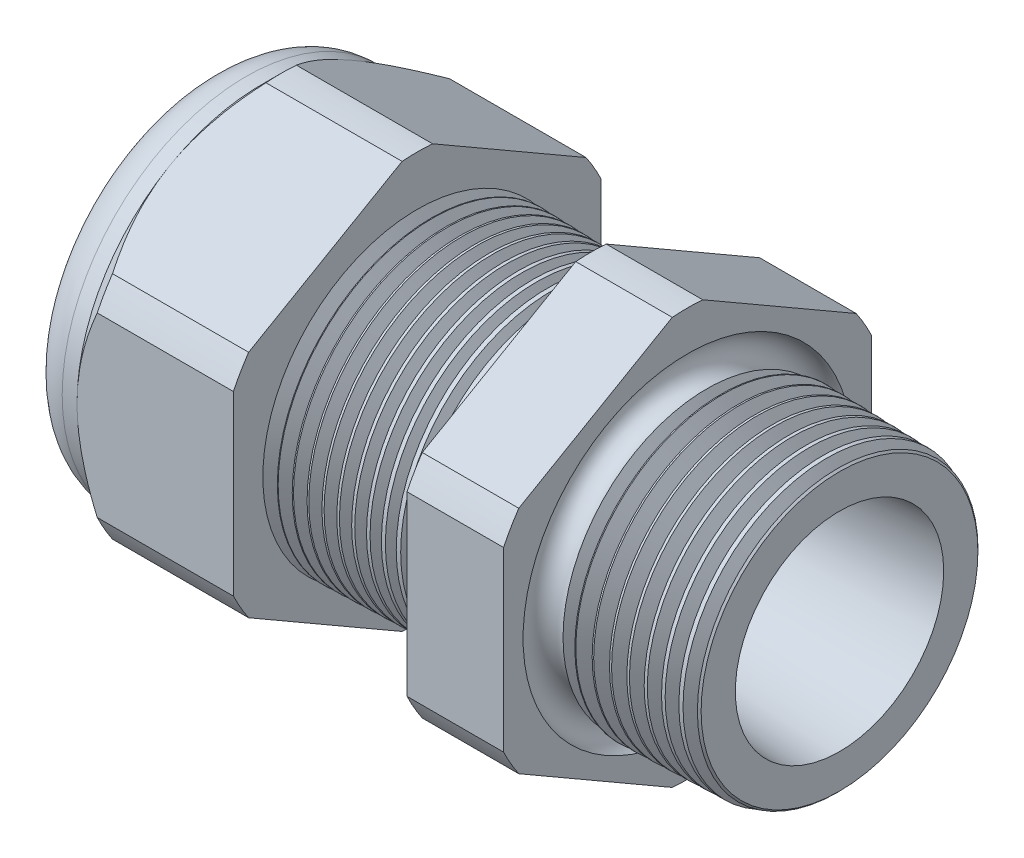
SolidWorks part; units mm, degrees
ref_plane "Front Plane" through (0, 0, 0) normal (0, 0, 1) x (1, 0, 0)
ref_plane "Top Plane" through (0, 0, 0) normal (0, 1, 0) x (1, 0, 0)
ref_plane "Right Plane" through (0, 0, 0) normal (1, 0, 0) x (0, 0, -1)
sketch "Sketch10" plane through (0, 0, 0) normal (0, 0, 1) x (1, 0, 0)
  line L0 (0, 0) -> (-115.3565, 0) construction
  line L1 (-32.766, 3.937) -> (-21.866, 3.937)
  line L2 (0, 5.3964) -> (0, 7.4284)
  line L3 (-7.874, 7.6346) -> (0, 7.4284)
  line L4 (-7.874, 19.05) -> (-7.874, 7.6346)
  line L5 (-7.874, 19.05) -> (-12.874, 19.05)
  line L6 (-12.874, 19.05) -> (-12.874, 7.7655)
  line L7 (-21.866, 8.001) -> (-12.874, 7.7655)
  line L8 (-21.866, 8.001) -> (-21.866, 19.05)
  line L9 (-21.866, 19.05) -> (-29.966, 19.05)
  line L10 (-29.966, 19.05) -> (-29.966, 9.525)
  line L11 (-29.966, 9.525) -> (-32.766, 9.525)
  line L12 (-32.766, 9.525) -> (-32.766, 3.937)
  line L13 (-21.866, 3.937) -> (0, 5.3964)
  dimension "D1" = 32.766
  dimension "D2" = 7.874
  dimension "D3" = 1.5
  dimension "D4" = 2.032
  dimension "A" = 16.002
  dimension "D6" = 19.05
  dimension "D8" = 38.1
  dimension "D9" = 2.8
  dimension "D10" = 8.1
  dimension "D11" = 5
  dimension "D" = 7.874
revolve "Revolve2" add sketch "Sketch10" angle 360 about L0
sketch "Sketch12" plane through (-29.966, 0, 0) normal (-1, 0, 0) x (0, 0, 1)
  line L1 (-0.7885, 10.5433) -> (-8.7365, 5.9545)
  line L2 (-9.525, 4.5888) -> (-9.525, -4.5888)
  line L3 (-8.7365, -5.9545) -> (-0.7885, -10.5433)
  line L4 (0.7885, -10.5433) -> (8.7365, -5.9545)
  line L5 (9.525, -4.5888) -> (9.525, 4.5888)
  line L6 (8.7365, 5.9545) -> (0.7885, 10.5433)
  circle A0 centre (0, 0) radius 9.525 construction
  arc A1 (0.7885, 10.5433) -> (-0.7885, 10.5433) centre (0, 0) ccw
  arc A2 (-8.7365, 5.9545) -> (-9.525, 4.5888) centre (0, 0) ccw
  arc A3 (-9.525, -4.5888) -> (-8.7365, -5.9545) centre (0, 0) ccw
  arc A4 (-0.7885, -10.5433) -> (0.7885, -10.5433) centre (0, 0) ccw
  arc A5 (8.7365, -5.9545) -> (9.525, -4.5888) centre (0, 0) ccw
  arc A6 (9.525, 4.5888) -> (8.7365, 5.9545) centre (0, 0) ccw
  dimension "D2" = 21.1455
  dimension "D1" = 19.05
extrude "Cut-Extrude2" cut sketch "Sketch12" against normal through all flip side to cut
fillet "Fillet4" radius 2.032 1 edges at (-32.766, 0, -9.525)
sketch "Sketch19" plane through (-29.966, 0, 0) normal (-1, 0, 0) x (0, 0, 1)
  line L0 (9.525, 0) -> (9.525, 4.5888) construction
  circle A0 centre (0, 0) radius 9.525
extrude "Cut-Extrude3" cut sketch "Sketch19" against normal blind 2 draft 45 flip side to cut
chamfer "Chamfer1" distance 0.254 angle 45 1 edges at (0, 0, -7.4284)
sketch "Sketch21" plane through (-32.766, 0, 0) normal (-1, 0, 0) x (0, 0, 1)
  circle A0 centre (0, 0) radius 3.937
  circle A2 centre (0, 0) radius 3.937 construction
extrude "plug" add sketch "Sketch21" against normal blind 3.81 separate body
sketch "Sketch22" plane through (-32.766, 0, 0) normal (-1, 0, 0) x (0, 0, 1)
  circle A0 centre (0, 0) radius 3.683
  circle A1 centre (0, 0) radius 3.937 construction
  dimension "D1" = 0.254
extrude "Cut-Extrude4" cut sketch "Sketch22" against normal blind 0.508
sketch "Sketch27" plane through (-32.258, 0, 0) normal (-1, 0, 0) x (0, 0, 1)
  line L0 (-4.3624, 0) -> (4.3624, 0) construction
  circle A0 centre (-1.8979, 0) radius 1.778
  circle A1 centre (0, 0) radius 3.683 construction
  dimension "D1" = 0.0071
  dimension "holedia" = 3.556
extrude "plugholes" cut sketch "Sketch27" against normal through all
pattern_circular "CirPattern1" count 2 over 360 about axis through (0, 0, 0) along (1, 0, 0) of "plugholes"
sketch "Sketch28" [suppressed] plane through (-29.464, 0, 0) normal (-1, 0, 0) x (0, 0, 1)
  circle A0 centre (0, 0) radius 0.762
  dimension "midholedia" = 3.556
extrude "midhole" [suppressed] cut sketch "Sketch28" against normal through all
sketch "Sketch29" plane through (0, 0, 0) normal (0, 0, 1) x (1, 0, 0)
  line L0 (-21.866, 8.001) -> (-21.133, 7.9818)
  line L1 (-12.874, 7.7655) -> (-21.866, 8.001) construction
  line L2 (-21.133, 7.9818) -> (-21.5161, 7.3566)
  line L3 (-21.5161, 7.3566) -> (-21.866, 8.001)
  dimension "D1" = 60
  dimension "D2" = 60
  dimension "D3" = 0.635
revolve "Cut-Revolve1" cut sketch "Sketch29" angle 360 about axis through (0, 0, 0) along (-1, 0, 0)
pattern_linear "LPattern1" count 12 spacing 0.762 along (1, 0, 0) of "Cut-Revolve1"
sketch "Sketch30" plane through (0, 0, 0) normal (0, 0, 1) x (1, 0, 0)
  line L0 (-7.874, 7.6346) -> (-6.9944, 7.6116)
  line L1 (-7.874, 10.5433) -> (-7.874, 5.9545) construction
  line L2 (-0.2539, 7.4351) -> (-7.874, 7.6346) construction
  line L3 (-6.9944, 7.6116) -> (-7.4542, 6.8614)
  line L4 (-7.4542, 6.8614) -> (-7.874, 7.6346)
  dimension "D1" = 60
  dimension "D2" = 60
  dimension "D3" = 0.762
revolve "Cut-Revolve2" cut sketch "Sketch30" angle 360 about axis through (0, 0, 0) along (-1, 0, 0)
pattern_linear "LPattern2" count 9 spacing 0.889 along (1, 0, 0) of "Cut-Revolve2"
sketch "Sketch31" [suppressed] plane through (-38.354, 0, 0) normal (-1, 0, 0) x (0, 0, 1)
  line L0 (-1.905, 1.905) -> (1.905, 1.905)
  line L1 (-1.905, -1.905) -> (1.905, -1.905)
  circle A0 centre (0, 0) radius 1.905 construction
  arc A1 (-1.905, 1.905) -> (-1.905, -1.905) centre (-1.905, 0) ccw
  arc A2 (1.905, 1.905) -> (1.905, -1.905) centre (1.905, 0) cw
extrude "Cut-Extrude5" [suppressed] cut sketch "Sketch31" against normal through all
sketch "Sketch32" plane through (0, 0, 0) normal (0, 0, 1) x (1, 0, 0)
  line L0 (-7.874, 10.5433) -> (-7.874, 5.9545) construction
  circle A0 centre (-7.747, 7.6346) radius 0.889
  dimension "D2" = 1.778
  dimension "D1" = 0.127
revolve "Cut-Revolve3" cut sketch "Sketch32" angle 360 about axis through (0, 0, 0) along (-1, 0, 0)
